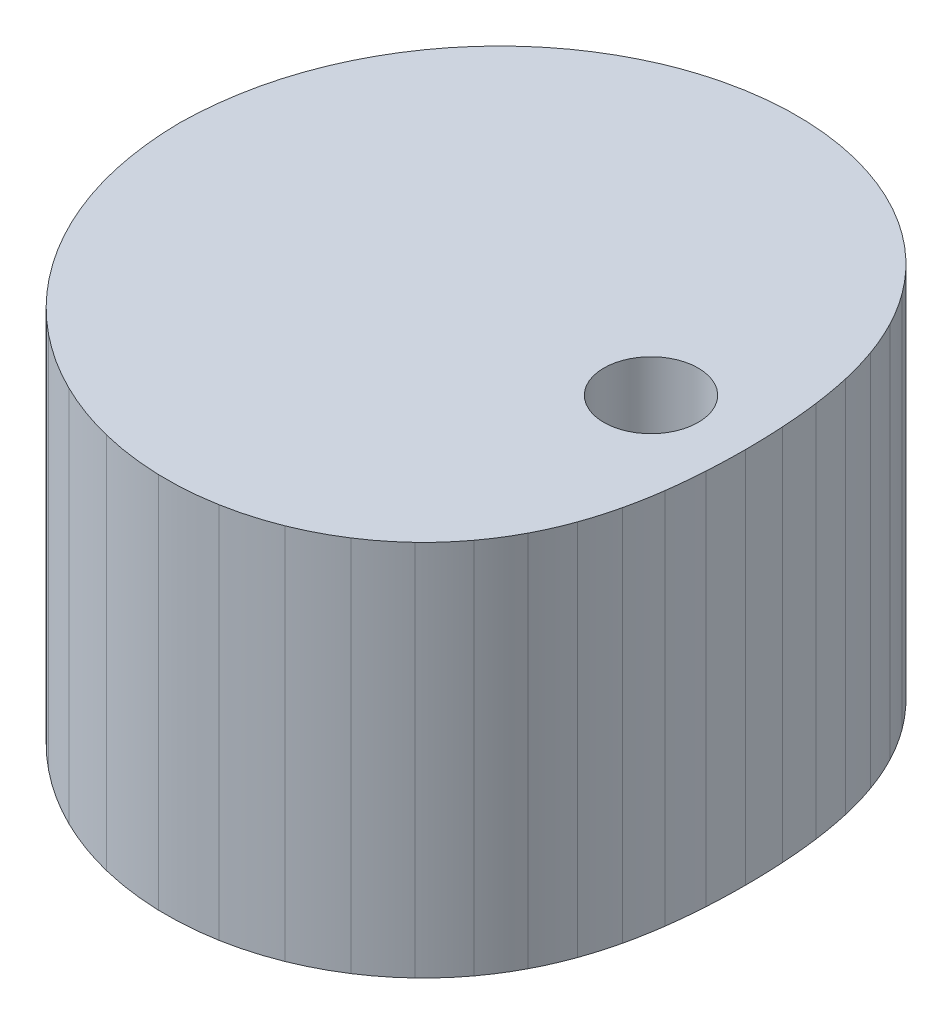
SolidWorks part; units mm, degrees
ref_plane "Front Plane" through (0, 0, 0) normal (0, 0, 1) x (1, 0, 0)
ref_plane "Top Plane" through (0, 0, 0) normal (0, 1, 0) x (1, 0, 0)
ref_plane "Right Plane" through (0, 0, 0) normal (1, 0, 0) x (0, 0, -1)
sketch "Sketch1" plane through (0, 0, 0) normal (0, 0, 1) x (1, 0, 0)
  line L0 (0, -1254) -> (0, 254) construction
  line L1 (3.175, 0) -> (127, 0)
  line L2 (127, 0) -> (127, -25.4)
  line L3 (127, -25.4) -> (3.175, -25.4)
  line L4 (3.175, -25.4) -> (3.175, 0)
revolve "Revolve1" add sketch "Sketch1" angle 360 about L0
sketch "Sketch2" plane through (0, 0, 0) normal (0, 1, 0) x (1, 0, 0)
  line L0 (0, 0) -> (19.05, 0) construction
  arc A0 (6.35, 0) -> (6.2725, 2.5671) centre (-37.8689, -0.0495) ccw
  arc A1 (6.2725, 2.5671) -> (6.0325, 5.0772) centre (-28.3406, 0.523) ccw
  arc A2 (6.0325, 5.0772) -> (5.5951, 7.5069) centre (-20.1864, 1.6117) ccw
  arc A3 (5.5951, 7.5069) -> (4.9083, 9.8665) centre (-14.9668, 2.802) ccw
  arc A4 (4.9083, 9.8665) -> (3.9033, 12.1717) centre (-12.2202, 3.7702) ccw
  arc A5 (3.9033, 12.1717) -> (2.5007, 14.4116) centre (-11.0177, 4.3875) ccw
  arc A6 (2.5007, 14.4116) -> (0.625, 16.5299) centre (-10.6832, 4.627) ccw
  arc A7 (0.625, 16.5299) -> (-1.7768, 18.4213) centre (-10.7813, 4.5168) ccw
  arc A8 (-1.7768, 18.4213) -> (-4.7158, 19.9411) centre (-11.0354, 4.1189) ccw
  arc A9 (-4.7158, 19.9411) -> (-8.1468, 20.9234) centre (-11.2745, 3.5161) ccw
  arc A10 (-8.1468, 20.9234) -> (-11.9616, 21.2051) centre (-11.4025, 2.8012) ccw
  arc A11 (-11.9616, 21.2051) -> (-15.9911, 20.6506) centre (-11.3806, 2.0651) ccw
  arc A12 (-15.9911, 20.6506) -> (-20.0172, 19.1748) centre (-11.2133, 1.3869) ccw
  arc A13 (-20.0172, 19.1748) -> (-23.7912, 16.7602) centre (-10.937, 0.8255) ccw
  arc A14 (-23.7912, 16.7602) -> (-27.0586, 13.4664) centre (-10.6072, 0.4141) ccw
  arc A15 (-27.0586, 13.4664) -> (-29.5855, 9.4302) centre (-10.287, 0.1577) ccw
  arc A16 (-29.5855, 9.4302) -> (-31.1833, 4.8563) centre (-10.0351, 0.0345) ccw
  arc A17 (-31.1833, 4.8563) -> (-31.75, 0) centre (-8.2041, -0.2865) ccw
  arc A18 (-31.75, 0) -> (-31.1833, -4.8563) centre (-8.2041, 0.2865) ccw
  arc A19 (-31.1833, -4.8563) -> (-29.5855, -9.4302) centre (-10.0351, -0.0345) ccw
  arc A20 (-29.5855, -9.4302) -> (-27.0586, -13.4664) centre (-10.287, -0.1577) ccw
  arc A21 (-27.0586, -13.4664) -> (-23.7912, -16.7602) centre (-10.6072, -0.4141) ccw
  arc A22 (-23.7912, -16.7602) -> (-20.0172, -19.1748) centre (-10.937, -0.8255) ccw
  arc A23 (-20.0172, -19.1748) -> (-15.9911, -20.6506) centre (-11.2133, -1.3869) ccw
  arc A24 (-15.9911, -20.6506) -> (-11.9616, -21.2051) centre (-11.3806, -2.0651) ccw
  arc A25 (-11.9616, -21.2051) -> (-8.1468, -20.9234) centre (-11.4025, -2.8012) ccw
  arc A26 (-8.1468, -20.9234) -> (-4.7158, -19.9411) centre (-11.2745, -3.5161) ccw
  arc A27 (-4.7158, -19.9411) -> (-1.7768, -18.4213) centre (-11.0354, -4.1189) ccw
  arc A28 (-1.7768, -18.4213) -> (0.625, -16.5299) centre (-10.7813, -4.5168) ccw
  arc A29 (0.625, -16.5299) -> (2.5007, -14.4116) centre (-10.6832, -4.627) ccw
  arc A30 (2.5007, -14.4116) -> (3.9033, -12.1717) centre (-11.0177, -4.3875) ccw
  arc A31 (3.9033, -12.1717) -> (4.9083, -9.8665) centre (-12.2202, -3.7702) ccw
  arc A32 (4.9083, -9.8665) -> (5.5951, -7.5069) centre (-14.9668, -2.802) ccw
  arc A33 (5.5951, -7.5069) -> (6.0325, -5.0772) centre (-20.1864, -1.6117) ccw
  arc A34 (6.0325, -5.0772) -> (6.2725, -2.5671) centre (-28.3406, -0.523) ccw
  arc A35 (6.2725, -2.5671) -> (6.35, 0) centre (-37.8689, 0.0495) ccw
extrude "Cut-Extrude1" cut sketch "Sketch2" along normal blind 10 and the other way blind 35.4 flip side to cut
